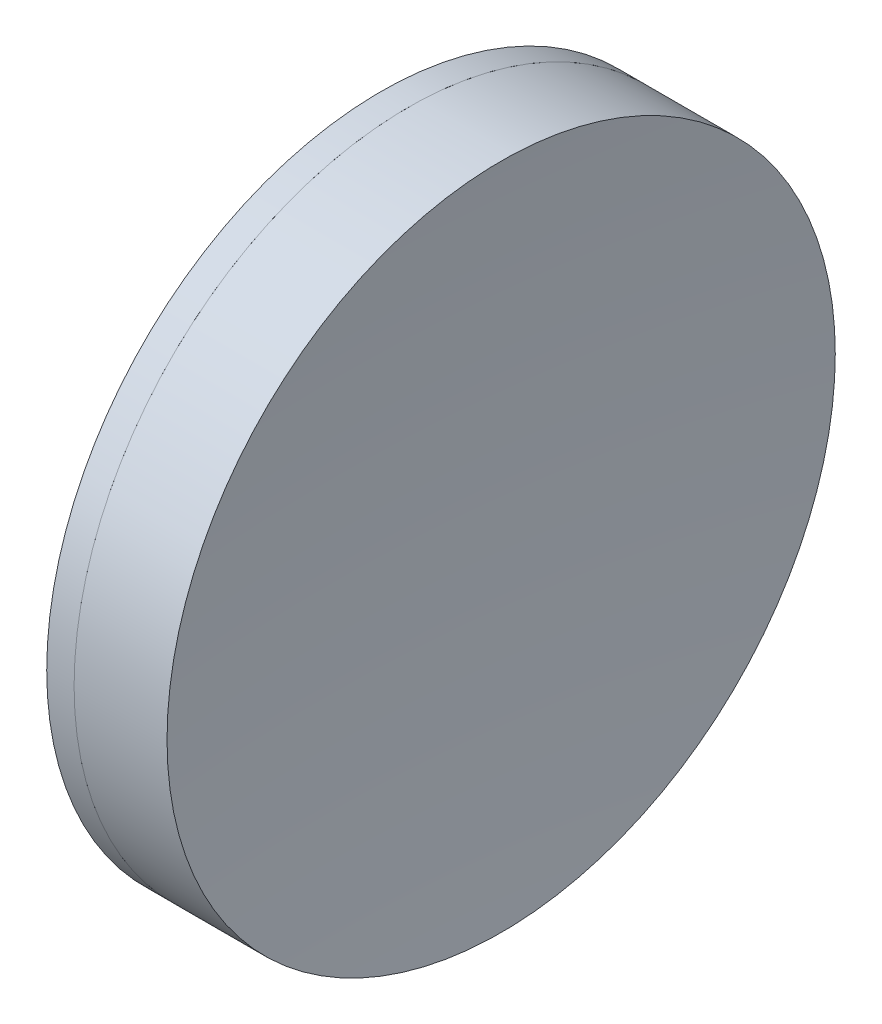
SolidWorks part; units mm, degrees
ref_plane "前视基准面" through (0, 0, 0) normal (0, 0, 1) x (1, 0, 0)
ref_plane "上视基准面" through (0, 0, 0) normal (0, 1, 0) x (1, 0, 0)
ref_plane "右视基准面" through (0, 0, 0) normal (1, 0, 0) x (0, 0, -1)
sketch "草图1" plane through (0, 0, 0) normal (0, 1, 0) x (1, 0, 0)
  line L0 (-0.8161, 0) -> (166.2668, 0) construction
  line L1 (151.5808, -25.4) -> (153.6622, -25.4)
  line L2 (151.5808, 25.4) -> (153.6622, 25.4)
  arc A0 (153.6622, -25.4) -> (153.6622, 25.4) centre (44.3648, 0) ccw
  arc A1 (151.5808, 25.4) -> (151.5808, -25.4) centre (241.8348, 0) ccw
  point P4 (166.2668, 0)
  point P10 (148.0748, 0)
  point P11 (156.5748, 0)
  dimension "D3" = 93.76
  dimension "D4" = 112.21
  dimension "D1" = 25.4
  dimension "D2" = 25.4
  dimension "D5" = 8.5
revolve "旋转1" add sketch "草图1" angle 360 about L0
sketch "草图2" plane through (0, 0, 0) normal (0, 1, 0) x (1, 0, 0)
  line L0 (-0.5519, 0) -> (162.8134, 0) construction
  line L2 (153.6622, 25.4) -> (160.7269, 25.4)
  line L3 (153.6622, -25.4) -> (160.7269, -25.4)
  arc A0 (160.7269, 25.4) -> (160.7269, -25.4) centre (440.1248, 0) ccw
  arc A1 (153.6622, -25.4) -> (153.6622, 25.4) centre (44.3648, 0) ccw construction
  arc A2 (153.6622, -25.4) -> (153.6622, 25.4) centre (44.3648, 0) ccw
  point P4 (156.5748, 0)
  point P8 (159.5748, 0)
  dimension "D1" = 280.55
  dimension "D2" = 3
revolve "旋转2" add sketch "草图2" angle 360 about L0
